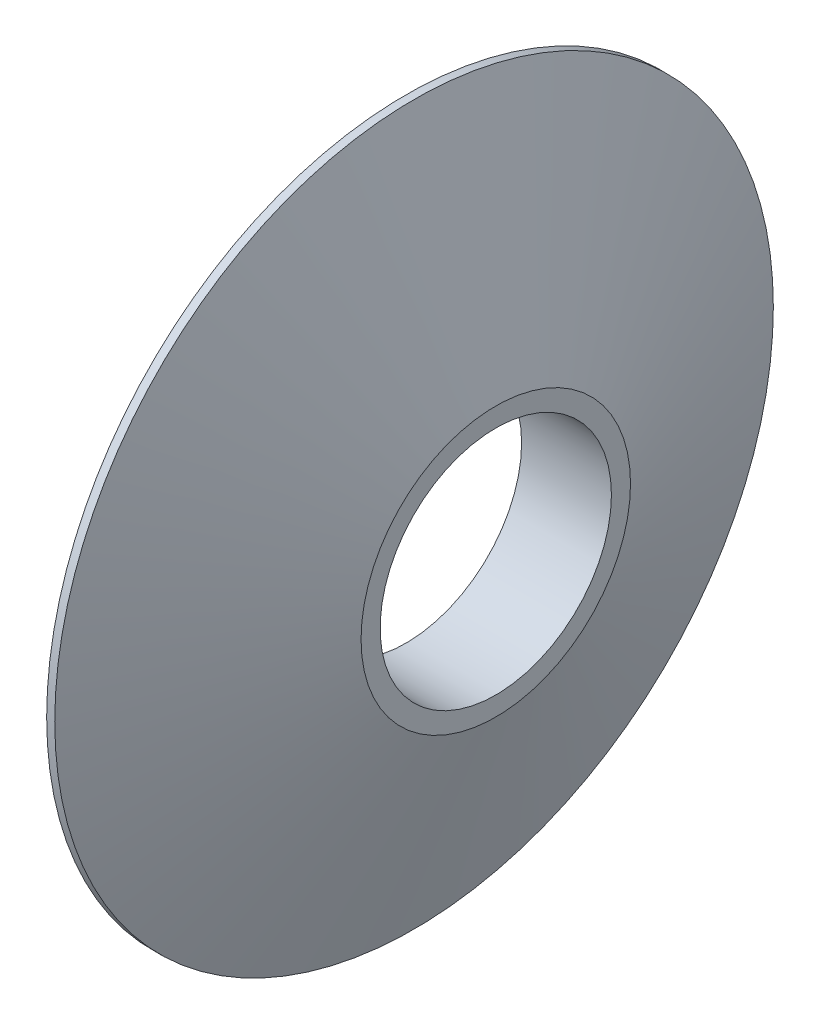
SolidWorks part; units mm, degrees
ref_plane "Front Plane" through (0, 0, 0) normal (0, 0, 1) x (1, 0, 0)
ref_plane "Top Plane" through (0, 0, 0) normal (0, 1, 0) x (1, 0, 0)
ref_plane "Right Plane" through (0, 0, 0) normal (1, 0, 0) x (0, 0, -1)
sketch "Sketch1" plane through (0, 0, 0) normal (0, 0, 1) x (1, 0, 0)
  line L0 (-13.2766, 0) -> (17.0213, 0) construction
  line L3 (0, 0) -> (0, 8)
  line L7 (2, 3) -> (2, 0)
  line L8 (2, 0) -> (0, 0)
  line L9 (0, 8) -> (0.1801, 8)
  line L10 (0.1801, 8) -> (2, 3)
  dimension "D1" = 8
  dimension "D2" = 2
  dimension "D3" = 5
  dimension "D4" = 160
revolve "Revolve1" add sketch "Sketch1" angle 360 about L0
sketch "Sketch2" plane through (2, 0, 0) normal (1, 0, 0) x (0, 0, -1)
  line L2 (-0.25, 2.2361) -> (-0.25, 2.4861)
  line L3 (-0.25, 2.4861) -> (0.25, 2.4861)
  line L4 (0.25, 2.2361) -> (0.25, 2.4861)
  line L5 (0, 2.25) -> (0.25, 2.4861) construction
  line L6 (-0.25, 2.4861) -> (0, 2.25) construction
  arc A0 (-0.25, 2.2361) -> (0.25, 2.2361) centre (0, 0) ccw
  point P3 (0, 2.25)
  dimension "D1" = 4.5
  dimension "D2" = 0.5
  dimension "D3" = 0.25
  dimension "D4" = 0.0139
extrude "Cut-Extrude1" [suppressed] cut sketch "Sketch2" against normal through all
sketch "Sketch5" plane through (2, 0, 0) normal (1, 0, 0) x (0, 0, -1)
  circle A0 centre (0, 0) radius 2.575
  dimension "D1" = 5.15
extrude "Cut-Extrude3" cut sketch "Sketch5" against normal through all
sketch "Sketch4" plane through (2, 0, 0) normal (1, 0, 0) x (0, 0, -1)
  circle A0 centre (0, 0) radius 3
  dimension "D1" = 6
extrude "Cut-Extrude2" [suppressed] cut sketch "Sketch4" against normal blind 0.5
